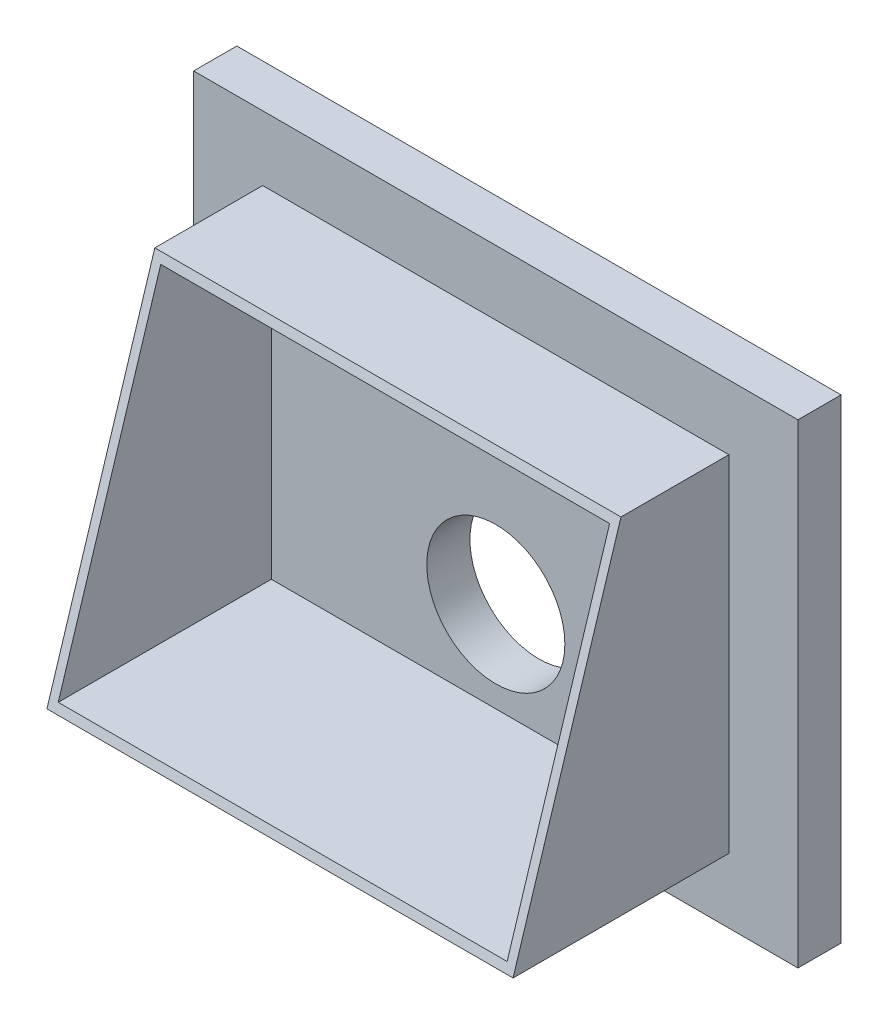
SolidWorks part; units mm, degrees
ref_plane "Front Plane" through (0, 0, 0) normal (0, 0, 1) x (1, 0, 0)
ref_plane "Top Plane" through (0, 0, 0) normal (0, 1, 0) x (1, 0, 0)
ref_plane "Right Plane" through (0, 0, 0) normal (1, 0, 0) x (0, 0, -1)
sketch "Sketch2" plane through (0, 0, 0) normal (0, 0, 1) x (1, 0, 0)
  line L1 (-350, -275) -> (350, -275)
  line L2 (-350, -275) -> (-350, 275)
  line L3 (-350, 275) -> (350, 275)
  line L4 (350, -275) -> (350, 275)
  line L5 (-350, -275) -> (350, 275) construction
  line L6 (-350, 275) -> (350, -275) construction
  point P0 (0, 0)
  dimension "D1" = 700
  dimension "D2" = 550
extrude "Boss-Extrude1" add sketch "Sketch2" along normal blind 50
sketch "Sketch3" plane through (0, 0, 50) normal (0, 0, 1) x (1, 0, 0)
  line L1 (-270, -200) -> (270, -200)
  line L2 (-270, -200) -> (-270, 200)
  line L3 (-270, 200) -> (270, 200)
  line L4 (270, -200) -> (270, 200)
  line L5 (-270, -200) -> (270, 200) construction
  line L6 (-270, 200) -> (270, -200) construction
  point P0 (0, 0)
  dimension "D1" = 400
  dimension "D2" = 540
extrude "Extrude-Thin1" add sketch "Sketch3" along normal blind 250 thin thin type one direction reverse wall 10
sketch "Sketch4" plane through (-270, 0, 0) normal (-1, 0, 0) x (0, 0, 1)
  line L0 (175, 200) -> (300, -200)
  line L1 (300, 200) -> (50, 200) construction
  line L2 (50, 275) -> (50, -275) construction
  line L3 (175, 200) -> (300, 200)
  line L4 (300, 200) -> (300, -200)
  dimension "D1" = 125
extrude "Cut-Extrude1" cut sketch "Sketch4" against normal through all
sketch "Sketch7" plane through (0, 0, 50) normal (0, 0, 1) x (1, 0, 0)
  line L0 (-350, -275) -> (350, -275) construction
  circle A0 centre (0, -85) radius 80
  dimension "D1" = 160
  dimension "D2" = 190
extrude "Cut-Extrude2" cut sketch "Sketch7" against normal through all
